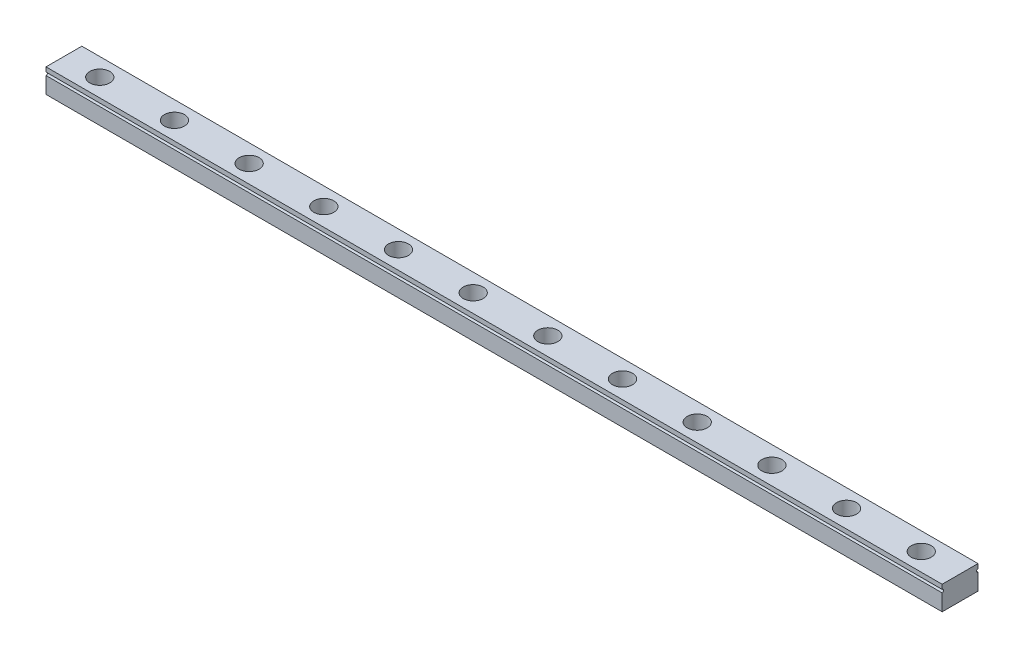
SolidWorks part; units mm, degrees
ref_plane "Front Plane" through (0, 0, 0) normal (0, 0, 1) x (1, 0, 0)
ref_plane "Top Plane" through (0, 0, 0) normal (0, 1, 0) x (1, 0, 0)
ref_plane "Right Plane" through (0, 0, 0) normal (1, 0, 0) x (0, 0, -1)
sketch "Sketch1" plane through (0, 0, 0) normal (1, 0, 0) x (0, 0, -1)
  line L0 (6, 8) -> (6, 0) construction
  line L1 (0, 0) -> (12, 0)
  line L2 (0, 0) -> (0, 8)
  line L3 (0, 8) -> (12, 8)
  line L4 (12, 0) -> (12, 8)
  arc A0 (0, 6.5) -> (0, 5.5) centre (0, 6) cw
  arc A1 (12, 6.5) -> (12, 5.5) centre (12, 6) ccw
  point P5 (0, 6)
  dimension "D4" = 0.5
  dimension "D1" = 12
  dimension "D2" = 8
  dimension "D3" = 6
extrude "Boss-Extrude1" add sketch "Sketch1" against normal blind 300 contours L0 L3 L2 A0 L1 | L3 L0 L1 L4 A1
hole_wizard "CBORE for M3 Button Head Screw1" positions "Sketch2" profile "Sketch3" counterbore size "M3" standard "JIS" end condition through all
sketch "Sketch2" plane through (0, 8, 0) normal (0, 1, 0) x (1, 0, 0)
  line L0 (-300, 0) -> (-300, 12) construction
  point P6 (-288, 6)
  dimension "D1" = 12
sketch "Sketch3" plane through (-288, 8, -6) normal (1, 0, 0) x (0, 0, 1)
  line L0 (0, 0) -> (0, 8)
  line L1 (0, 8) -> (1.7, 8)
  line L3 (1.7, 8) -> (1.7, 6.15)
  line L4 (1.7, 6.15) -> (3.35, 6.15)
  line L5 (3.35, 6.15) -> (3.35, 0)
  line L7 (3.35, 0) -> (0, 0)
  line L11 (0, -6.35) -> (0, 107.95) construction
  dimension "Thru Hole Dia." = 3.4
  dimension "Thru Hole Depth" = 8
  dimension "C'Bore Dia." = 6.7
  dimension "C'Bore Depth" = 6.15
pattern_linear "LPattern1" count 12 spacing 25 along (1, 0, 0) of "CBORE for M3 Button Head Screw1"
